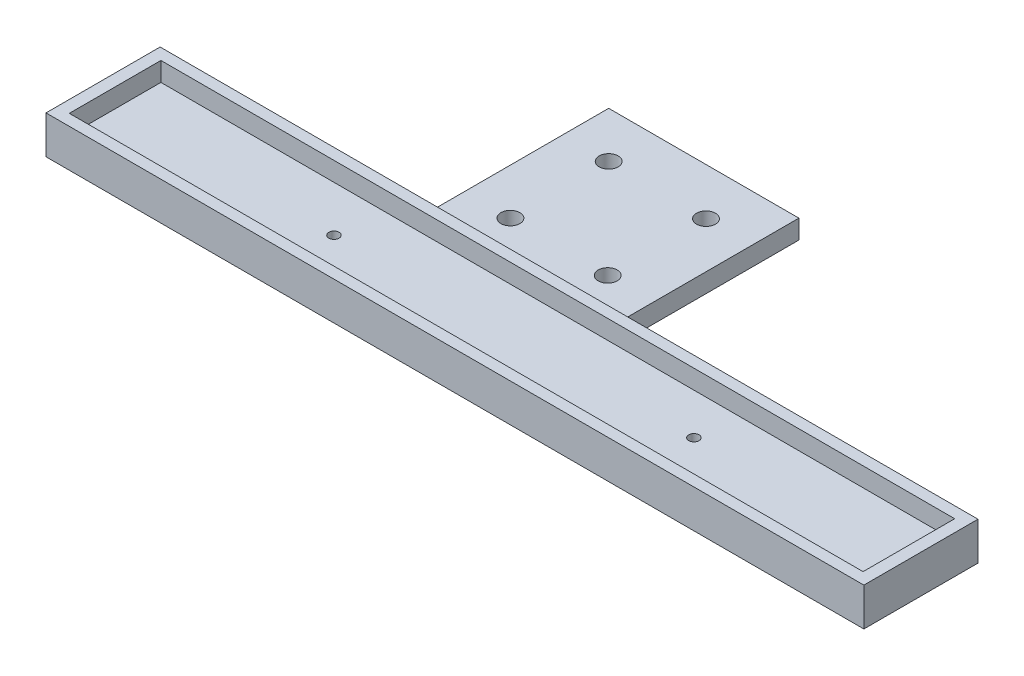
SolidWorks part; units mm, degrees
ref_plane "Front Plane" through (0, 0, 0) normal (0, 0, 1) x (1, 0, 0)
ref_plane "Top Plane" through (0, 0, 0) normal (0, 1, 0) x (1, 0, 0)
ref_plane "Right Plane" through (0, 0, 0) normal (1, 0, 0) x (0, 0, -1)
sketch "Sketch1" plane through (0, 0, 0) normal (0, 1, 0) x (1, 0, 0)
  line L1 (62.6, -7.225) -> (-62.6, -7.225)
  line L2 (62.6, -7.225) -> (62.6, 7.225)
  line L3 (62.6, 7.225) -> (-62.6, 7.225)
  line L4 (-62.6, -7.225) -> (-62.6, 7.225)
  line L5 (62.6, -7.225) -> (-62.6, 7.225) construction
  line L6 (62.6, 7.225) -> (-62.6, -7.225) construction
  line L7 (64.5, -9) -> (-64.5, -9)
  line L8 (64.5, -9) -> (64.5, 9)
  line L9 (64.5, 9) -> (-64.5, 9)
  line L10 (-64.5, -9) -> (-64.5, 9)
  line L11 (64.5, -9) -> (-64.5, 9) construction
  line L12 (64.5, 9) -> (-64.5, -9) construction
  point P0 (0, 0)
  point P6 (0, 0)
  dimension "D1" = 14.45
  dimension "D2" = 18
  dimension "D3" = 125.2
  dimension "D4" = 129
extrude "Boss-Extrude1" add sketch "Sketch1" along normal blind 3
sketch "Sketch2" plane through (0, 0, 0) normal (0, -1, 0) x (1, 0, 0)
  line L1 (64.5, 9) -> (-64.5, 9)
  line L2 (64.5, 9) -> (64.5, -9)
  line L3 (64.5, -9) -> (-64.5, -9)
  line L4 (-64.5, 9) -> (-64.5, -9)
  point P6 (0, 0)
  point P7 (0, 0)
  point P8 (0, 0)
  point P9 (0, -28.2518)
  point P11 (0, 0)
  point P12 (0, 0)
extrude "Boss-Extrude2" add sketch "Sketch2" along normal blind 3
sketch "Sketch4" plane through (0, 0, 0) normal (0, 1, 0) x (1, 0, 0)
  line L0 (62.6, -7.225) -> (62.6, 7.225) construction
  line L1 (62.6, 7.225) -> (-62.6, 7.225) construction
  line L2 (-62.6, 7.225) -> (-62.6, -7.225) construction
  circle A0 centre (27.97, 0.725) radius 0.81
  circle A1 centre (-28.08, 0) radius 0.81
  dimension "D4" = 1.62
  dimension "D5" = 1.62
  dimension "D1" = 34.63
  dimension "D2" = 6.5
  dimension "D3" = 34.52
extrude "Cut-Extrude1" cut sketch "Sketch4" against normal through all
sketch "Sketch5" plane through (0, -3, 0) normal (0, -1, 0) x (1, 0, 0)
  line L0 (-64.5, -9) -> (64.5, -9) construction
  line L1 (-23.75, -9) -> (6.25, -9)
  line L2 (-23.75, -9) -> (-23.75, -39)
  line L3 (-23.75, -39) -> (6.25, -39)
  line L4 (6.25, -9) -> (6.25, -39)
  line L5 (62.6, 7.225) -> (62.6, -7.225) construction
  circle A0 centre (-1, -16.0927) radius 1.5
  circle A1 centre (-1.0008, -31.5927) radius 1.5
  circle A2 centre (-16.5, -31.75) radius 1.5
  circle A3 centre (-16.4992, -16.25) radius 1.5
  point P8 (-8.75, -39)
  point P18 (0, 0)
  point P20 (-8.75, 0)
  dimension "D5" = 3
  dimension "D6" = 3
  dimension "D7" = 3
  dimension "D8" = 3
  dimension "D1" = 30
  dimension "D2" = 30
  dimension "D3" = 15.5
  dimension "D4" = 15.5
  dimension "D9" = 15.5
  dimension "D10" = 15.5
  dimension "D11" = 7.25
  dimension "D12" = 7.25
  dimension "D13" = 71.35
extrude "Boss-Extrude4" add sketch "Sketch5" against normal blind 3
